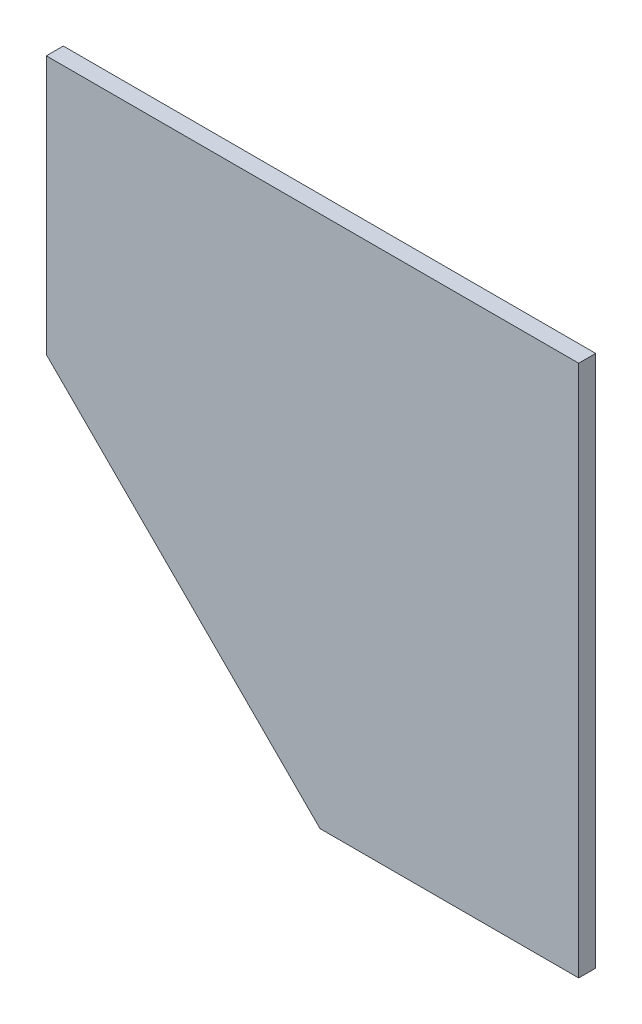
SolidWorks part; units mm, degrees
ref_plane "Front Plane" through (0, 0, 0) normal (0, 0, 1) x (1, 0, 0)
ref_plane "Top Plane" through (0, 0, 0) normal (0, 1, 0) x (1, 0, 0)
ref_plane "Right Plane" through (0, 0, 0) normal (1, 0, 0) x (0, 0, -1)
sketch "Sketch1" plane through (0, 0, 0) normal (0, 0, 1) x (1, 0, 0)
  line L0 (-282, -186.5) -> (8, -476.5)
  line L1 (282, -476.5) -> (8, -476.5)
  line L2 (282, -476.5) -> (282, 87.5)
  line L3 (282, 87.5) -> (-282, 87.5)
  line L4 (-282, -186.5) -> (-282, 87.5)
  point P0 (0, 0)
  dimension "D1" = 274
  dimension "D2" = 564
extrude "Boss-Extrude1" add sketch "Sketch1" along normal blind 18
equation "\"H_DSP\"=18"
equation "\"D1@Boss-Extrude1\"=\"H_DSP\""
